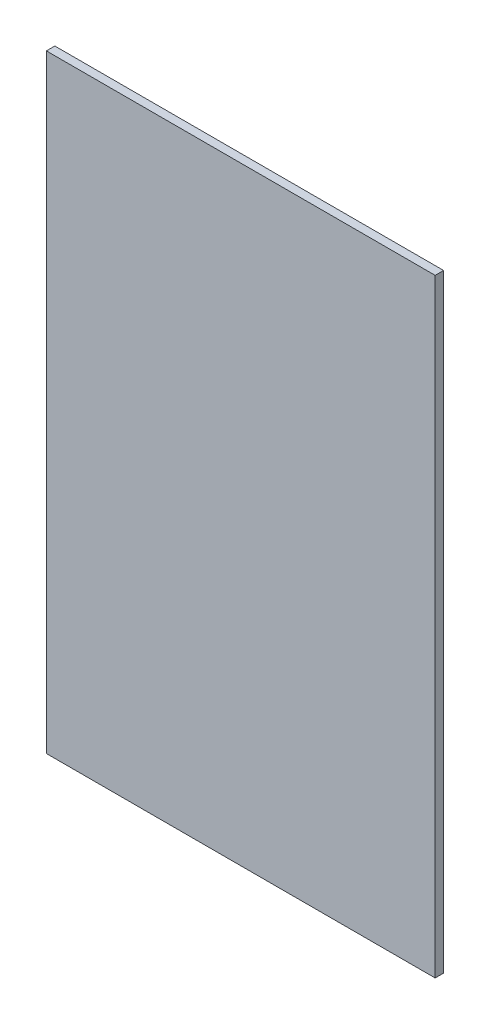
SolidWorks part; units mm, degrees
ref_plane "Front Plane" through (0, 0, 0) normal (0, 0, 1) x (1, 0, 0)
ref_plane "Top Plane" through (0, 0, 0) normal (0, 1, 0) x (1, 0, 0)
ref_plane "Right Plane" through (0, 0, 0) normal (1, 0, 0) x (0, 0, -1)
sketch "Sketch1" plane through (0, 0, 0) normal (0, 0, 1) x (1, 0, 0)
  line L1 (-292.1, -457.2) -> (292.1, -457.2)
  line L2 (-292.1, -457.2) -> (-292.1, 457.2)
  line L3 (-292.1, 457.2) -> (292.1, 457.2)
  line L4 (292.1, -457.2) -> (292.1, 457.2)
  line L5 (-292.1, -457.2) -> (292.1, 457.2) construction
  line L6 (-292.1, 457.2) -> (292.1, -457.2) construction
  point P0 (0, 0)
  dimension "D1" = 584.2
  dimension "D2" = 914.4
extrude "Boss-Extrude1" add sketch "Sketch1" along normal blind 12.7
